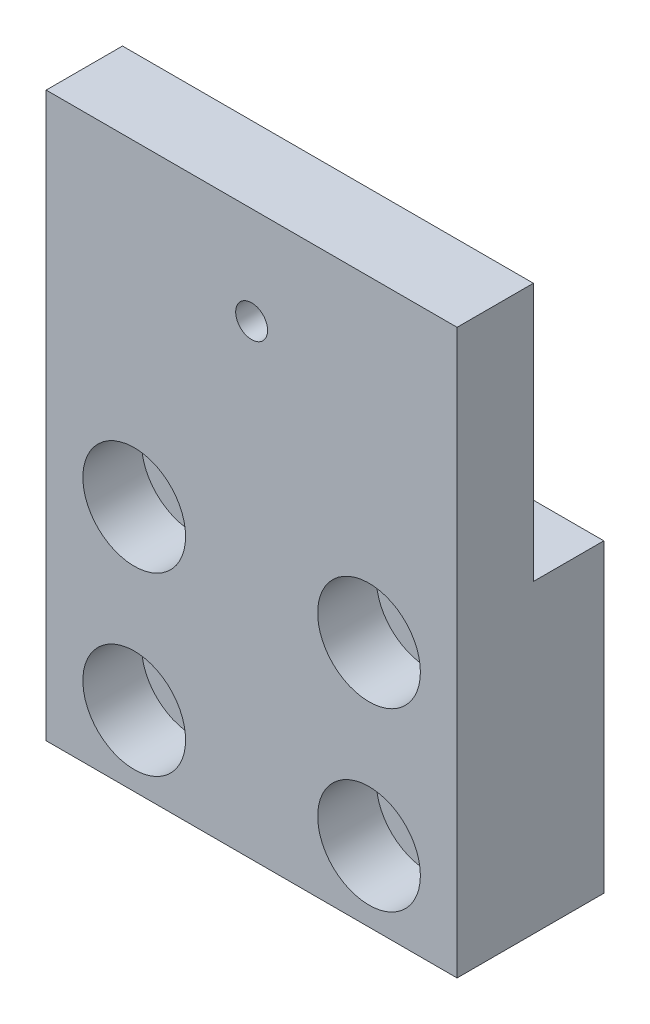
SolidWorks part; units mm, degrees
ref_plane "Front Plane" through (0, 0, 0) normal (0, 0, 1) x (1, 0, 0)
ref_plane "Top Plane" through (0, 0, 0) normal (0, 1, 0) x (1, 0, 0)
ref_plane "Right Plane" through (0, 0, 0) normal (1, 0, 0) x (0, 0, -1)
sketch "Sketch1" plane through (0, 0, 0) normal (0, 0, 1) x (1, 0, 0)
  line L1 (-22.225, 30.48) -> (22.225, 30.48)
  line L2 (-22.225, 30.48) -> (-22.225, -30.48)
  line L3 (-22.225, -30.48) -> (22.225, -30.48)
  line L4 (22.225, 30.48) -> (22.225, -30.48)
  dimension "D1" = 22.225
  dimension "D2" = 22.225
  dimension "D3" = 30.48
  dimension "D4" = 30.48
extrude "Boss-Extrude1" add sketch "Sketch1" along normal mid plane 15.875
hole_wizard "CBORE for 1/4 Socket Head Cap Screw1" positions "Sketch3" profile "Sketch2" counterbore size "1/4" standard "ANSI Inch" end condition through all
sketch "Sketch3" plane through (0, 0, 7.9375) normal (0, 0, 1) x (1, 0, 0)
  line L0 (-22.225, -30.48) -> (22.225, -30.48) construction
  point P0 (-12.7, -3.81)
  point P2 (12.7, -3.81)
  point P4 (12.7, -22.86)
  point P6 (-12.7, -22.86)
  dimension "D1" = 19.05
  dimension "D2" = 7.62
  dimension "D3" = 12.7
  dimension "D4" = 12.7
sketch "Sketch2" plane through (-12.7, -3.81, 7.9375) normal (1, 0, 0) x (0, -1, 0)
  line L0 (0, 0) -> (0, 15.875)
  line L1 (0, 15.875) -> (3.3782, 15.875)
  line L3 (3.3782, 15.875) -> (3.3782, 6.35)
  line L4 (3.3782, 6.35) -> (5.5562, 6.35)
  line L5 (5.5562, 6.35) -> (5.5562, 0)
  line L7 (5.5562, 0) -> (0, 0)
  line L11 (0, -6.35) -> (0, 107.95) construction
  dimension "Thru Hole Dia." = 6.7564
  dimension "Thru Hole Depth" = 15.875
  dimension "C'Bore Dia." = 11.1125
  dimension "C'Bore Depth" = 6.35
sketch "Sketch4" plane through (22.225, 0, 0) normal (1, 0, 0) x (0, 0, -1)
  line L1 (7.9375, 30.48) -> (0.3175, 30.48)
  line L2 (7.9375, 30.48) -> (7.9375, 2.54)
  line L3 (7.9375, 2.54) -> (0.3175, 2.54)
  line L4 (0.3175, 30.48) -> (0.3175, 2.54)
  dimension "D1" = 7.62
  dimension "D2" = 27.94
extrude "Cut-Extrude1" cut sketch "Sketch4" against normal through all
hole_wizard "#8-32 Tapped Hole1" positions "Sketch6" profile "Sketch5" tap size "#8-32" standard "ANSI Inch" end condition through all
sketch "Sketch6" plane through (0, 0, 7.9375) normal (0, 0, 1) x (1, 0, 0)
  circle A0 centre (12.7, -3.81) radius 3.3782 construction
  point P2 (0, 19.939)
  point P9 (0, 0)
  dimension "D1" = 0
  dimension "D3" = 23.749
sketch "Sketch5" plane through (0, 19.939, 7.9375) normal (1, 0, 0) x (0, -1, 0)
  line L0 (0, 0) -> (0, 15.875)
  line L1 (0, 15.875) -> (1.7272, 15.875)
  line L2 (1.7272, 15.875) -> (1.7272, 0)
  line L5 (1.7272, 0) -> (0, 0)
  line L11 (0, -6.35) -> (0, 107.95) construction
  dimension "Thru Tap Drill Dia." = 3.4544
  dimension "Thru Tap Drill Depth" = 15.875
cosmetic thread "Hole Thread1" parameters "D2"=4.1656
